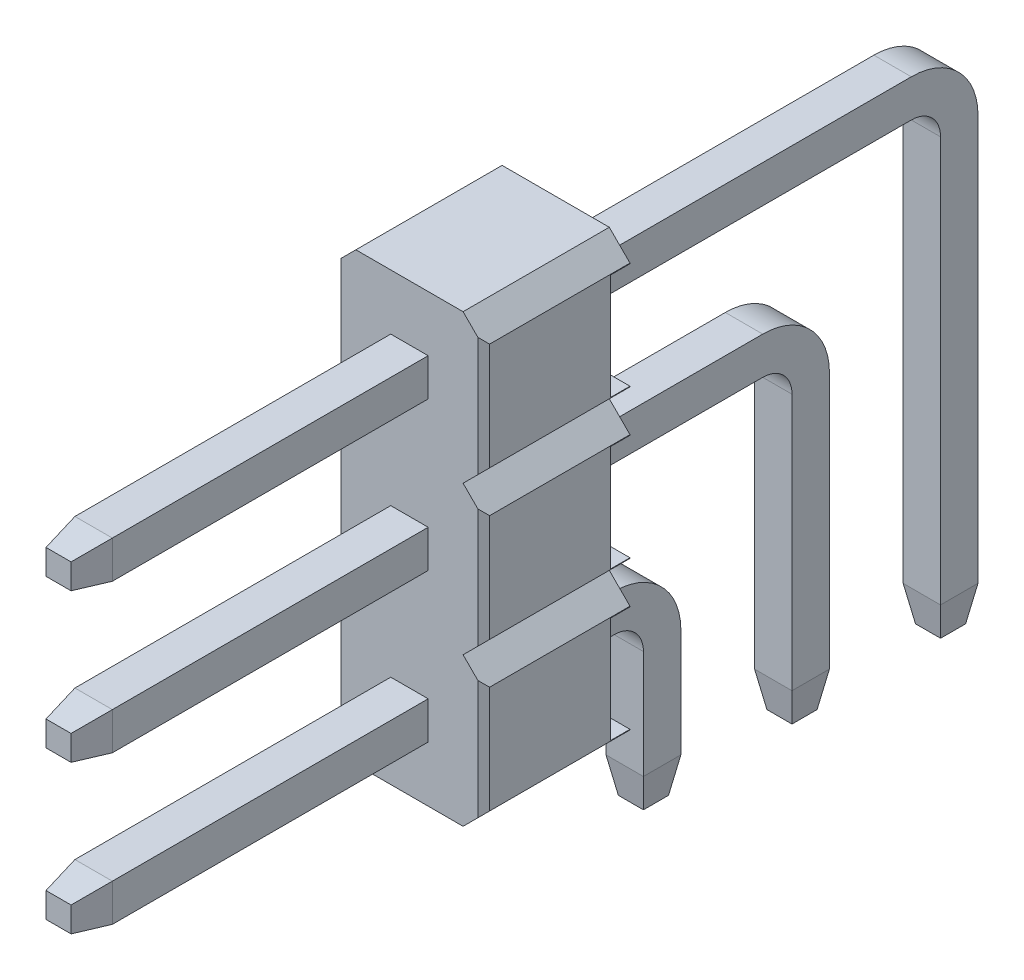
SolidWorks part; units mm, degrees
ref_plane "Plan de face" through (0, 0, 0) normal (0, 0, 1) x (1, 0, 0)
ref_plane "Plan de dessus" through (0, 0, 0) normal (0, 1, 0) x (1, 0, 0)
ref_plane "Plan de droite" through (0, 0, 0) normal (1, 0, 0) x (0, 0, -1)
sketch "Esquisse1" plane through (0, 0, 0) normal (0, 0, 1) x (1, 0, 0)
  line L0 (0, 1.27) -> (0, 0) construction
  line L1 (-0.9164, 1.27) -> (0.9164, 1.27)
  line L2 (-1.27, 0.9164) -> (-1.27, -0.9164)
  line L3 (1.27, 0.9164) -> (1.27, -0.9164)
  line L4 (1.27, 0.9164) -> (0.9164, 1.27)
  line L5 (-0.9164, -1.27) -> (0.9164, -1.27)
  line L6 (-1.27, 0.9164) -> (-0.9164, 1.27)
  line L7 (-1.0932, 1.0932) -> (0, 0) construction
  line L8 (-1.27, 0.9164) -> (-1.27, 1.27) construction
  line L9 (-0.9164, 1.27) -> (-1.27, 1.27) construction
  line L10 (1.27, -0.9164) -> (0.9164, -1.27)
  line L11 (-1.27, -0.9164) -> (-0.9164, -1.27)
  line L17 (1.27, 0.9164) -> (1.27, -0.9164)
  line L20 (-1.27, 0) -> (0, 0) construction
  line L33 (3.81, -0.9164) -> (3.4564, -1.27) [skipped]
  line L34 (3.81, 0.9164) -> (3.81, -0.9164) [skipped]
  line L35 (3.81, 0.9164) -> (3.4564, 1.27) [skipped]
  line L36 (1.6236, 1.27) -> (3.4564, 1.27) [skipped]
  line L37 (1.6236, -1.27) -> (3.4564, -1.27) [skipped]
  line L38 (6.35, -0.9164) -> (5.9964, -1.27) [skipped]
  line L39 (6.35, 0.9164) -> (6.35, -0.9164) [skipped]
  line L40 (6.35, 0.9164) -> (5.9964, 1.27) [skipped]
  line L41 (4.1636, 1.27) -> (5.9964, 1.27) [skipped]
  line L42 (3.81, 0.9164) -> (4.1636, 1.27) [skipped]
  line L43 (3.81, 0.9164) -> (3.81, -0.9164) [skipped]
  line L44 (3.81, -0.9164) -> (4.1636, -1.27) [skipped]
  line L45 (4.1636, -1.27) -> (5.9964, -1.27) [skipped]
  line L46 (1.27, 0.9164) -> (1.6236, 1.27) [skipped]
  line L47 (1.27, -0.9164) -> (1.6236, -1.27) [skipped]
  point P14 (1.27, 0)
  point P23 (0, 0)
  dimension "D1" = 1.27
  dimension "D2" = 45
  dimension "D3" = 0.25
  dimension "D4" = 3
extrude "Boss.-Extru.1" add sketch "Esquisse1" along normal mid plane 2.5
sketch "Esquisse2" plane through (1.27, 0, 0) normal (1, 0, 0) x (0, 0, -1)
  line L1 (1.25, 0.9064) -> (0.92, 0.9064)
  line L2 (1.25, 0.9064) -> (1.25, -0.9064)
  line L3 (1.25, -0.9064) -> (0.92, -0.9064)
  line L4 (0.92, 0.9064) -> (0.92, -0.9064)
  line L7 (0, 0) -> (1.25, 0) construction
  line L8 (-1.25, 0.9164) -> (1.25, 0.9164) construction
  line L9 (-1.25, 0.9164) -> (1.25, 0.9164) construction
  line L10 (1.25, 0.9164) -> (1.25, -0.9164) construction
  dimension "D1" = 0.33
  dimension "D2" = 0.02
extrude "Enlèv. mat.-Extru.2" cut sketch "Esquisse2" against normal through all
chamfer "Chanfrein1" distance 0.1 angle 45 2 edges at (-1.27, 0, 1.25) (1.27, 0, 1.25)
pattern_linear "Répétition linéaire1" count 3 spacing 2.54 along (0, 1, 0) of "Boss.-Extru.1", "Enlèv. mat.-Extru.2", "Chanfrein1"
sketch "Esquisse3" plane through (0, 0, 0) normal (1, 0, 0) x (0, 0, -1)
  line L0 (-7.25, 0) -> (2.75, 0) construction
  line L1 (2.75, 0) -> (2.75, -3.27) construction
  line L2 (-7.25, -0.32) -> (-7.25, 0.32)
  line L3 (-7.25, 0.32) -> (1.93, 0.32)
  line L4 (3.07, -0.82) -> (3.07, -3.27)
  line L5 (3.07, -3.27) -> (2.43, -3.27)
  line L6 (2.43, -3.27) -> (2.43, -0.82)
  line L7 (1.93, -0.32) -> (-7.25, -0.32)
  line L8 (1.25, -0.9164) -> (1.25, -1.27) construction
  line L9 (-1.25, -1.0164) -> (-1.25, 1.0164) construction
  line L10 (-1.25, -1.27) -> (1.25, -1.27) construction
  line L11 (-7.25, 2.86) -> (4.47, 2.86)
  line L12 (-7.25, 2.22) -> (-7.25, 2.86)
  line L13 (4.47, 2.22) -> (-7.25, 2.22)
  line L14 (-7.25, 5.4) -> (7.01, 5.4)
  line L15 (-7.25, 4.76) -> (-7.25, 5.4)
  line L16 (7.01, 4.76) -> (-7.25, 4.76)
  line L17 (-7.25, 2.54) -> (5.29, 2.54) construction
  line L18 (-7.25, 5.08) -> (7.83, 5.08) construction
  line L19 (5.29, 2.54) -> (5.29, -3.27) construction
  line L20 (7.83, 5.08) -> (7.83, -3.27) construction
  line L21 (5.29, 0) -> (5.29, -3.27) construction
  line L22 (7.83, 0) -> (7.83, -3.27) construction
  line L23 (4.97, -3.27) -> (5.61, -3.27)
  line L24 (7.51, -3.27) -> (8.15, -3.27)
  line L25 (4.97, -3.27) -> (4.97, 1.72)
  line L26 (5.61, -3.27) -> (5.61, 1.72)
  line L27 (7.51, -3.27) -> (7.51, 4.26)
  line L28 (8.15, -3.27) -> (8.15, 4.26)
  arc A0 (2.43, -0.82) -> (1.93, -0.32) centre (1.93, -0.82) ccw
  arc A1 (1.93, 0.32) -> (3.07, -0.82) centre (1.93, -0.82) cw
  arc A2 (7.01, 5.4) -> (8.15, 4.26) centre (7.01, 4.26) cw
  arc A3 (4.47, 2.86) -> (5.61, 1.72) centre (4.47, 1.72) cw
  arc A4 (7.01, 4.76) -> (7.51, 4.26) centre (7.01, 4.26) cw
  arc A5 (4.47, 2.22) -> (4.97, 1.72) centre (4.47, 1.72) cw
  point P6 (-7.25, 0)
  point P9 (2.75, -3.27)
  point P12 (1.25, -1.0932)
  point P43 (7.83, -3.27)
  point P44 (5.29, -3.27)
  dimension "D5" = 0.5
  dimension "D6" = 1.14
  dimension "D11" = 1.14
  dimension "D12" = 0.5
  dimension "D1" = 1.5
  dimension "D2" = 6
  dimension "D3" = 0.64
  dimension "D4" = 2
  dimension "D8" = 2.54
  dimension "D9" = 2.54
  dimension "D10" = 2.54
  dimension "D7" = 3
extrude "Boss.-Extru.2" add sketch "Esquisse3" along normal mid plane 0.64
chamfer "Chanfrein2" distance 0.6 angle 10 24 edges at (0, -3.27, -7.51) (0.32, -3.27, -7.83) (0, -3.27, -8.15) (-0.32, -3.27, -7.83) (0, -3.27, -2.43) (0.32, -3.27, -2.75) (0, -3.27, -3.07) (-0.32, -3.27, -2.75) (0, -3.27, -4.97) (0.32, -3.27, -5.29) (0, -3.27, -5.61) (-0.32, -3.27, -5.29) (0, 5.4, 7.25) (0.32, 5.08, 7.25) (0, 4.76, 7.25) (-0.32, 5.08, 7.25) (0, 2.86, 7.25) (0.32, 2.54, 7.25) (0, 2.22, 7.25) (-0.32, 2.54, 7.25) (0, 0.32, 7.25) (0.32, 0, 7.25) (0, -0.32, 7.25) (-0.32, 0, 7.25)
